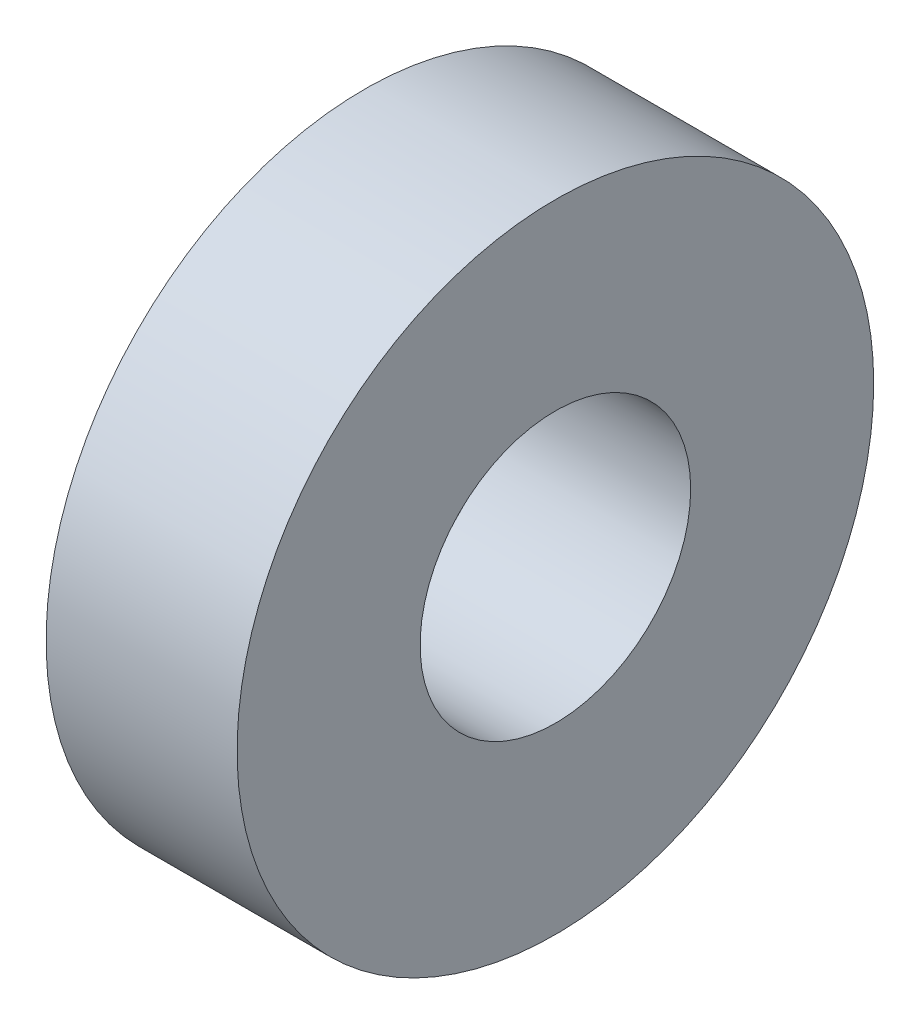
SolidWorks part; units mm, degrees
material "AISI 304"
ref_plane "Front" through (0, 0, 0) normal (0, 0, 1) x (1, 0, 0)
ref_plane "Top" through (0, 0, 0) normal (0, 1, 0) x (1, 0, 0)
ref_plane "Right" through (0, 0, 0) normal (1, 0, 0) x (0, 0, -1)
sketch "Sketch1" plane through (0, 0, 0) normal (1, 0, 0) x (0, 0, -1)
  circle A0 centre (0, 0) radius 8.5
  circle A1 centre (0, 0) radius 20
  dimension "I.D." = 17
  dimension "O.D." = 40
extrude "Extrude1" add sketch "Sketch1" along normal mid plane 12
